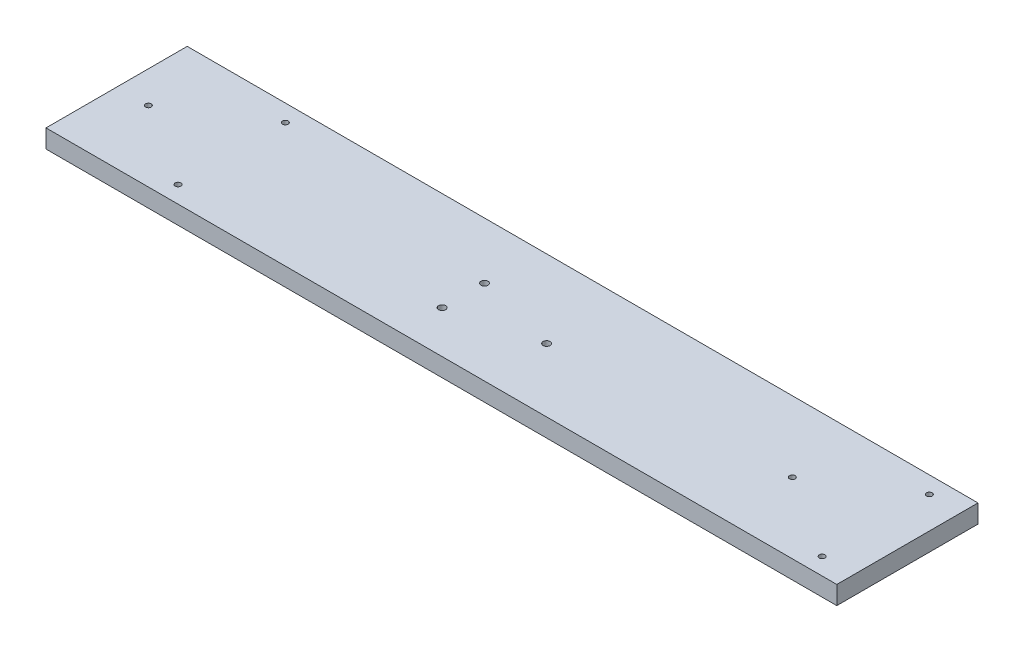
SolidWorks part; units mm, degrees
ref_plane "Front Plane" through (0, 0, 0) normal (0, 0, 1) x (1, 0, 0)
ref_plane "Top Plane" through (0, 0, 0) normal (0, 1, 0) x (1, 0, 0)
ref_plane "Right Plane" through (0, 0, 0) normal (1, 0, 0) x (0, 0, -1)
sketch "Sketch1" plane through (0, 0, 0) normal (0, 1, 0) x (1, 0, 0)
  line L1 (0, 0) -> (280, 0)
  line L2 (0, 0) -> (0, 50)
  line L3 (0, 50) -> (280, 50)
  line L4 (280, 0) -> (280, 50)
extrude "Boss-Extrude1" add sketch "Sketch1" along normal blind 6.5
sketch "Sketch2" plane through (0, 0, 0) normal (0, -1, 0) x (-1, 0, 0)
  circle A8 centre (-125.25, 30) radius 1.25
  circle A9 centre (-125.25, 15) radius 1.25
  circle A10 centre (-154.75, 22.5) radius 1.25
extrude "Cut-Extrude1" cut sketch "Sketch2" against normal through all
sketch "Sketch3" plane through (0, 0, 0) normal (0, -1, 0) x (1, 0, 0)
  line L0 (269.5, -41.5) -> (268, -41.5) construction
  line L1 (268, -8.5) -> (269.5, -8.5) construction
  circle A0 centre (268.7985, -44) radius 1
  circle A2 centre (268.7985, -6) radius 1
  circle A3 centre (239.25, -25) radius 1
  circle A4 centre (11.25, -25) radius 1
  circle A5 centre (40.75, -6) radius 1
  circle A6 centre (40.75, -44) radius 1
  dimension "D1" = 2.5
  dimension "D2" = 2.5
extrude "Cut-Extrude2" cut sketch "Sketch3" against normal through all
